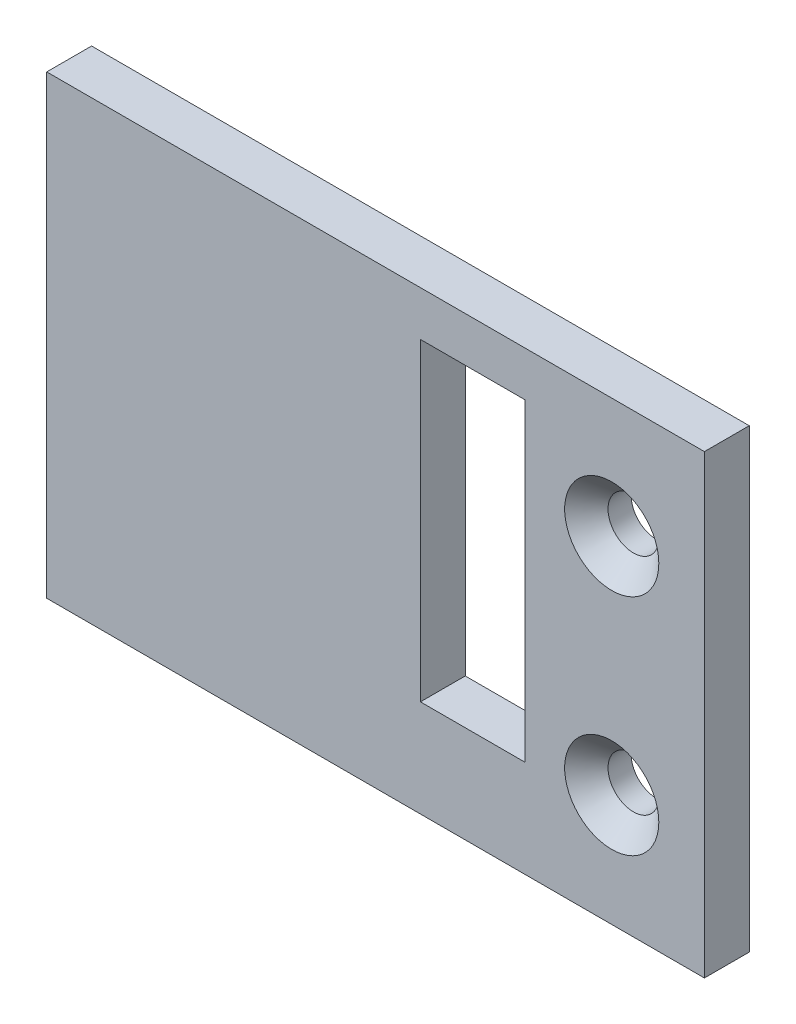
SolidWorks part; units mm, degrees
ref_plane "Front Plane" through (0, 0, 0) normal (0, 0, 1) x (1, 0, 0)
ref_plane "Top Plane" through (0, 0, 0) normal (0, 1, 0) x (1, 0, 0)
ref_plane "Right Plane" through (0, 0, 0) normal (1, 0, 0) x (0, 0, -1)
sketch "Sketch1" plane through (0, 0, 0) normal (0, 0, 1) x (1, 0, 0)
  line L1 (-6, 15.25) -> (6, 15.25)
  line L2 (-6, 15.25) -> (-6, -15.25)
  line L3 (-6, -15.25) -> (6, -15.25)
  line L4 (6, 15.25) -> (6, -15.25)
  line L5 (-6, 15.25) -> (6, -15.25) construction
  line L6 (-6, -15.25) -> (6, 15.25) construction
  line L7 (-6, -15.25) -> (-38, -15.25)
  line L8 (-6, -15.25) -> (-6, 15.25)
  line L9 (-6, 15.25) -> (-38, 15.25)
  line L10 (-38, -15.25) -> (-38, 15.25)
  line L11 (-6, -8.75) -> (-13, -8.75)
  line L12 (-6, -8.75) -> (-6, 12.25)
  line L13 (-6, 12.25) -> (-13, 12.25)
  line L14 (-13, -8.75) -> (-13, 12.25)
  circle A0 centre (-0.2, -7.75) radius 1.4205
  circle A1 centre (-0.2, 7.25) radius 1.384
  point P0 (0, 0)
  dimension "D1" = 12
  dimension "D2" = 30.5
  dimension "D3" = 6.2
  dimension "D4" = 7.5
  dimension "D5" = 15
  dimension "D6" = 6.2
  dimension "D7" = 32
  dimension "D8" = 7
  dimension "D9" = 6.5
  dimension "D10" = 21
extrude "Boss-Extrude1" add sketch "Sketch1" along normal blind 3 contours L11 L14 L13 L2 L9 L10 L7 L8 | L4 L1 L2 L8 L3 A1 A0
hole_wizard "CSK for M3 Flat Head Machine Screw1" positions "Sketch3" profile "Sketch4" countersink size "M3" standard "ANSI Metric" end condition through all
sketch "Sketch3" plane through (0, 0, 3) normal (0, 0, 1) x (1, 0, 0)
  point P0 (-0.2, 7.25)
  point P3 (-0.2, -7.75)
  point P7 (0, 0)
sketch "Sketch4" plane through (-0.2, 7.25, 3) normal (1, 0, 0) x (0, -1, 0)
  line L0 (0, 0) -> (0, 3)
  line L1 (0, 3) -> (1.7, 3)
  line L2 (1.7, 3) -> (1.7, 1.45)
  line L3 (1.7, 1.45) -> (3.15, 0)
  line L5 (3.15, 0) -> (0, 0)
  line L6 (-1.7, 1.45) -> (-3.15, 0) construction
  line L11 (0, -6.35) -> (0, 107.95) construction
  dimension "Thru Hole Dia." = 3.4
  dimension "Thru Hole Depth" = 3
  dimension "Near C'Sink Dia." = 6.3
  dimension "Near C'Sink Angle" = 90
